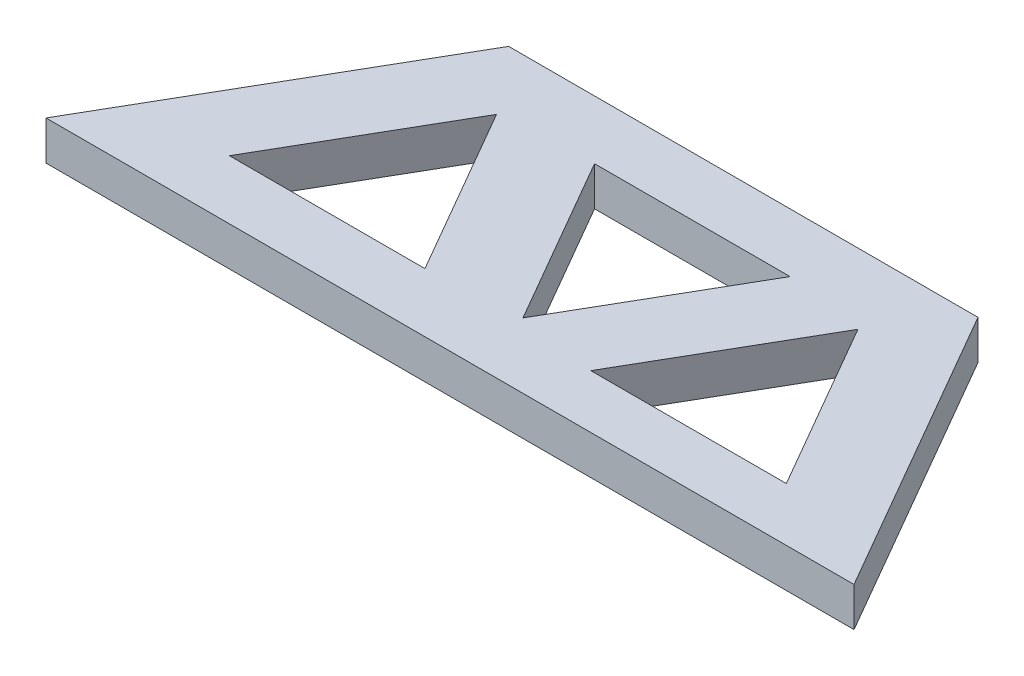
SolidWorks part; units mm, degrees
ref_plane "Front Plane" through (0, 0, 0) normal (0, 0, 1) x (1, 0, 0)
ref_plane "Top Plane" through (0, 0, 0) normal (0, 1, 0) x (1, 0, 0)
ref_plane "Right Plane" through (0, 0, 0) normal (1, 0, 0) x (0, 0, -1)
sketch "Sketch1" plane through (0, 0, 0) normal (0, 1, 0) x (1, 0, 0)
  line L0 (43.3013, 75) -> (0, 0)
  line L6 (80.254, 60) -> (130.254, 60)
  line L7 (130.254, 60) -> (105.254, 16.6987)
  line L9 (125.6016, 13.6952) -> (150.6016, 56.9965)
  line L10 (150.6016, 56.9965) -> (175.6016, 13.6952)
  line L12 (206.6025, 0) -> (163.3013, 75)
  line L13 (163.3013, 75) -> (43.3013, 75)
  line L14 (80.254, 60) -> (105.254, 16.6987)
  line L15 (125.6016, 13.6952) -> (175.6016, 13.6952)
  line L16 (206.6025, 0) -> (0, 0)
  line L17 (31.8044, 15.0868) -> (56.8044, 58.3881)
  line L18 (56.8044, 58.3881) -> (81.8044, 15.0868)
  line L19 (31.8044, 15.0868) -> (81.8044, 15.0868)
  dimension "D1" = 120
  dimension "D2" = 50
  dimension "D3" = 60
  dimension "D4" = 60
  dimension "D5" = 75
  dimension "D6" = 50
  dimension "D7" = 60
  dimension "D8" = 60
  dimension "D9" = 20
  dimension "D10" = 20
  dimension "D11" = 15
extrude "Boss-Extrude1" add sketch "Sketch1" along normal blind 10
sketch "Sketch2" plane through (0, 10, 0) normal (0, 1, 0) x (1, 0, 0)
  line L0 (10.9791, 7.8829) -> (198.4841, 7.8829) construction
  circle A0 centre (56.7501, 7.8829) radius 5.7273
  circle A1 centre (104.7316, 7.8829) radius 5.2169
  circle A2 centre (143.8748, 7.8829) radius 3.4292
